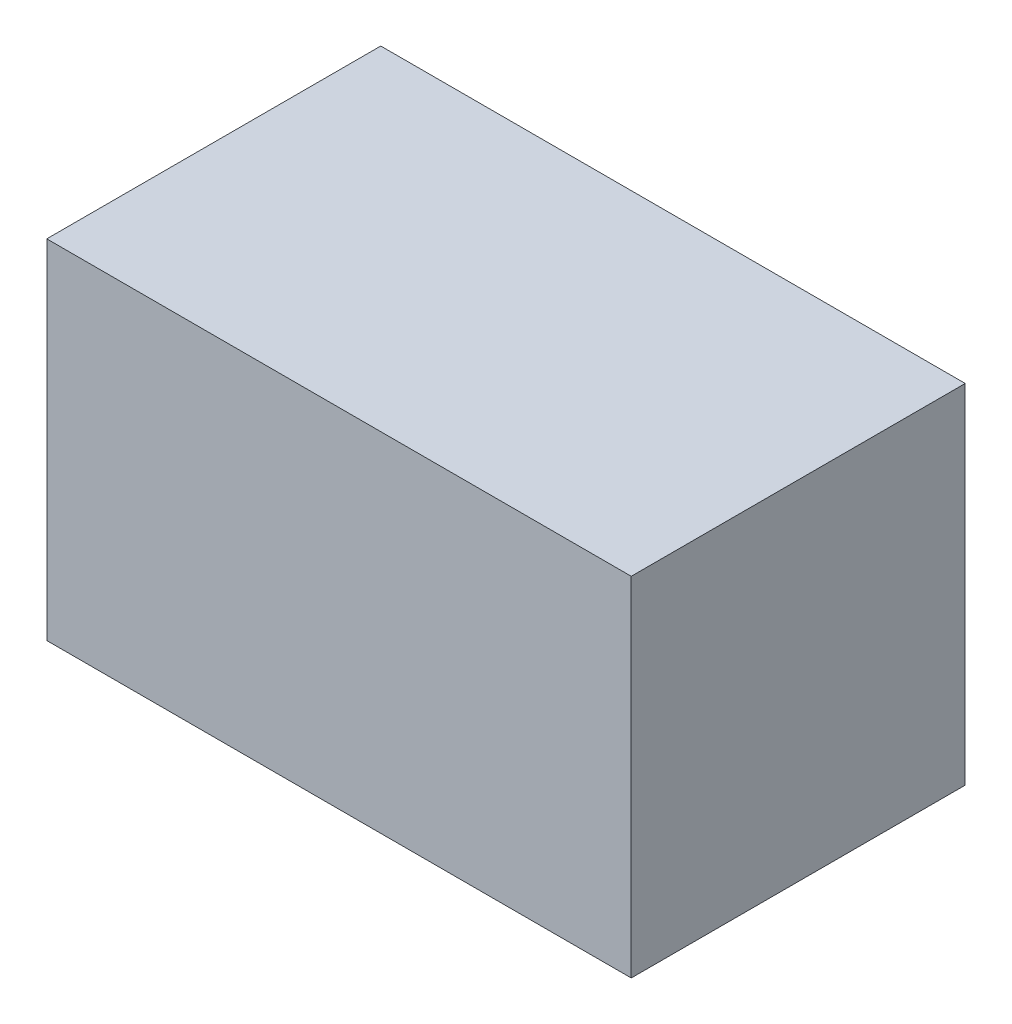
SolidWorks part; units mm, degrees
ref_plane "Front Plane" through (0, 0, 0) normal (0, 0, 1) x (1, 0, 0)
ref_plane "Top Plane" through (0, 0, 0) normal (0, 1, 0) x (1, 0, 0)
ref_plane "Right Plane" through (0, 0, 0) normal (1, 0, 0) x (0, 0, -1)
sketch "Sketch1" plane through (0, 0, 0) normal (0, 1, 0) x (1, 0, 0)
  line L1 (0, 0) -> (84, 0)
  line L2 (0, 0) -> (0, 48)
  line L3 (0, 48) -> (84, 48)
  line L4 (84, 0) -> (84, 48)
  dimension "D1" = 84
  dimension "D2" = 48
extrude "Boss-Extrude1" add sketch "Sketch1" along normal blind 50
